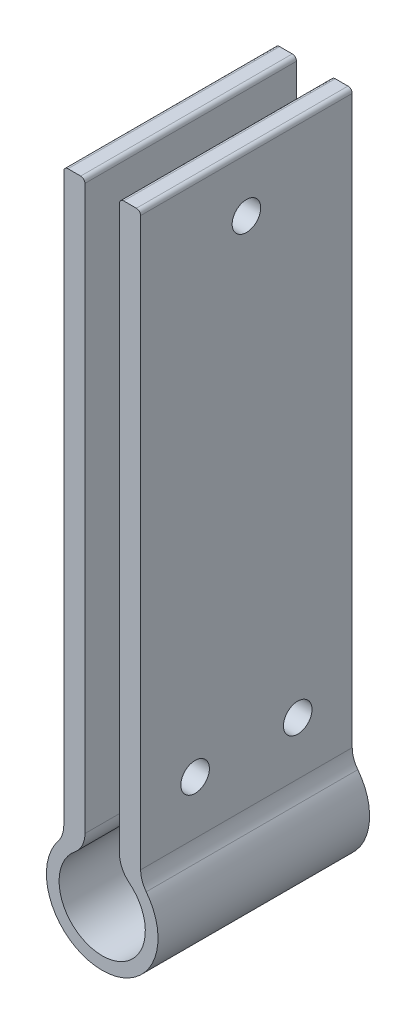
SolidWorks part; units mm, degrees
ref_plane "Plan de face" through (0, 0, 0) normal (0, 0, 1) x (1, 0, 0)
ref_plane "Plan de dessus" through (0, 0, 0) normal (0, 1, 0) x (1, 0, 0)
ref_plane "Plan de droite" through (0, 0, 0) normal (1, 0, 0) x (0, 0, -1)
sketch "Esquisse1" plane through (0, 0, 0) normal (0, 0, 1) x (1, 0, 0)
  line L1 (0, 0) -> (0, 27.5119) construction
  line L3 (-3.266, 7.467) -> (-3.266, 117.467)
  line L4 (-3.266, 117.467) -> (-7.266, 117.467)
  line L5 (-7.266, 117.467) -> (-7.266, 7.649)
  line L6 (3.266, 117.467) -> (7.266, 117.467)
  line L7 (7.266, 117.467) -> (7.266, 7.649)
  line L8 (3.266, 7.467) -> (3.266, 117.467)
  arc A0 (-3.266, 7.467) -> (3.266, 7.467) centre (0, 0) ccw
  arc A1 (-7.266, 7.649) -> (7.266, 7.649) centre (0, 0) ccw
  dimension "D1" = 16.3
  dimension "D2" = 2.4
  dimension "D3" = 110
  dimension "D4" = 4
  dimension "D5" = 6.532
extrude "Boss.-Extru.1" add sketch "Esquisse1" along normal blind 40
fillet "Congé1" radius 5 4 edges at (-3.266, 7.467, 20) (3.266, 7.467, 20) (-7.266, 7.649, 20) (7.266, 7.649, 20)
fillet "Congé2" radius 0.8 4 edges at (-7.266, 117.467, 20) (-3.266, 117.467, 20) (3.266, 117.467, 20) (7.266, 117.467, 20)
hole_wizard "Dégagement M1.61" positions "Esquisse2" profile "Esquisse4" hole size "M1.6" standard "Ansi Metric" end condition through all
sketch "Esquisse2" plane through (-7.266, 0, 0) normal (-1, 0, 0) x (0, 0, 1)
  line L0 (20, 9.5576) -> (20, 116.667) construction
  line L1 (0, 9.5576) -> (40, 9.5576) construction
  line L2 (40, 116.667) -> (0, 116.667) construction
  line L4 (20, 19.6228) -> (40, 19.6228) construction
  line L5 (40, 116.667) -> (40, 9.5576) construction
  line L7 (20, 19.6228) -> (0, 19.6228) construction
  line L8 (0, 116.667) -> (0, 9.5576) construction
  point P0 (20, 106.5945)
  point P5 (10.2996, 19.6228)
  point P36 (29.7004, 19.6228)
  point P37 (20, 106.5945)
sketch "Esquisse4" plane through (-7.266, 106.5945, 20) normal (0, 1, 0) x (0, 0, 1)
  line L0 (0, 0) -> (0, 17.816)
  line L1 (0, 17.816) -> (2.7, 17.816)
  line L2 (2.7, 17.816) -> (2.7, 0)
  line L5 (2.7, 0) -> (0, 0)
  line L11 (0, -6.35) -> (0, 107.95) construction
  dimension "Diamètre du perçage jusqu'au prochain" = 5.4
  dimension "Profondeur du perçage jusqu'au prochain" = 17.816
